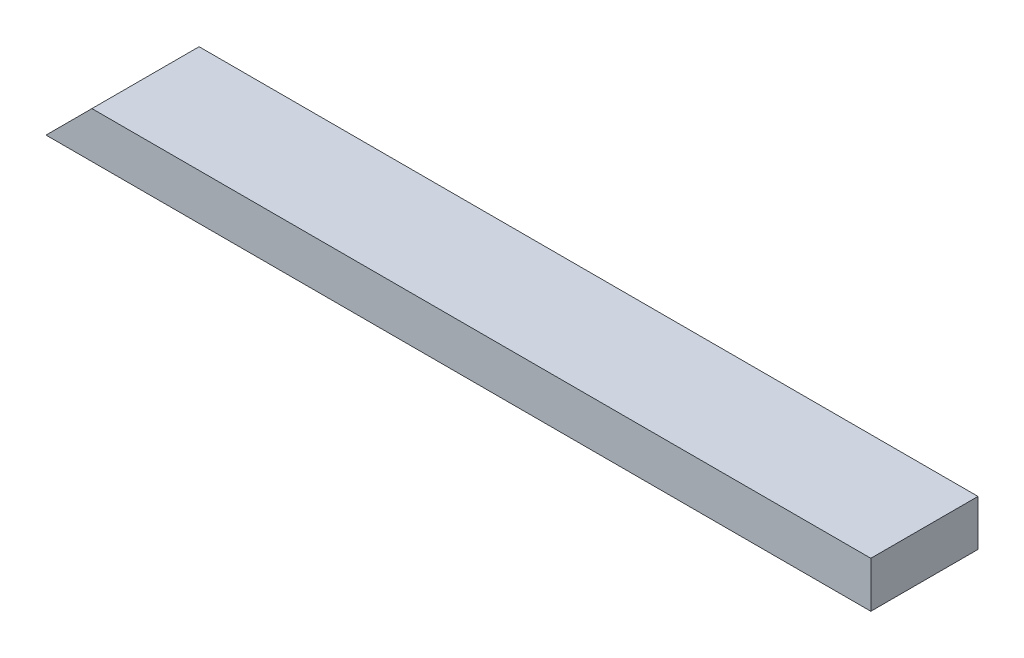
SolidWorks part; units mm, degrees
material "Pine"
ref_plane "Front Plane" through (0, 0, 0) normal (0, 0, 1) x (1, 0, 0)
ref_plane "Top Plane" through (0, 0, 0) normal (0, 1, 0) x (1, 0, 0)
ref_plane "Right Plane" through (0, 0, 0) normal (1, 0, 0) x (0, 0, -1)
sketch "Sketch1" plane through (0, 0, 0) normal (0, 1, 0) x (1, 0, 0)
  line L1 (0, 0) -> (684.2442, 0)
  line L2 (0, 0) -> (0, 88.9)
  line L3 (0, 88.9) -> (684.2442, 88.9)
  line L4 (684.2442, 0) -> (684.2442, 88.9)
  dimension "D1" = 88.9
  dimension "D2" = 684.2442
extrude "Boss-Extrude1" add sketch "Sketch1" along normal blind 38.1
sketch "Sketch2" plane through (0, 0, 0) normal (0, 0, 1) x (1, 0, 0)
  line L0 (0, 0) -> (38.1, 38.1)
  line L1 (0, 38.1) -> (684.2442, 38.1) construction
  line L2 (0, 38.1) -> (0, 0)
  line L6 (38.1, 38.1) -> (0, 38.1)
  dimension "D1" = 38.1
extrude "Cut-Extrude1" cut sketch "Sketch2" against normal through all
